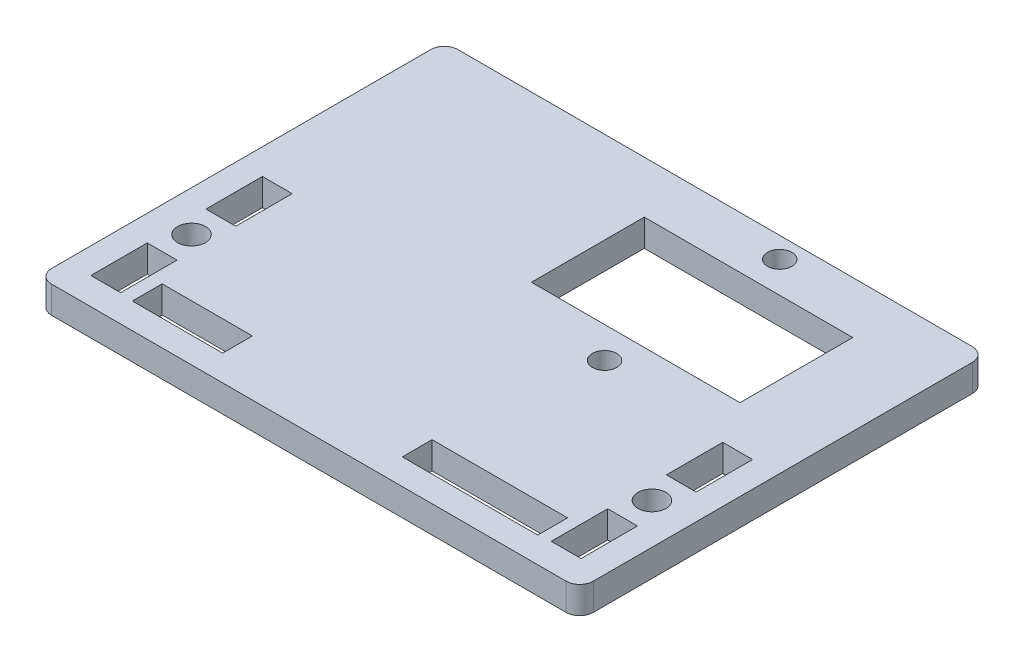
SolidWorks part; units mm, degrees
ref_plane "Front Plane" through (0, 0, 0) normal (0, 0, 1) x (1, 0, 0)
ref_plane "Top Plane" through (0, 0, 0) normal (0, 1, 0) x (1, 0, 0)
ref_plane "Right Plane" through (0, 0, 0) normal (1, 0, 0) x (0, 0, -1)
sketch "Sketch1" plane through (0, 0, 0) normal (0, 1, 0) x (1, 0, 0)
  line L1 (1.5, 0) -> (58.5, 0)
  line L2 (0, 1.5) -> (0, 43.5)
  line L3 (1.5, 45) -> (58.5, 45)
  line L4 (60, 1.5) -> (60, 43.5)
  arc A0 (1.5, 0) -> (0, 1.5) centre (1.5, 1.5) cw
  arc A1 (58.5, 0) -> (60, 1.5) centre (58.5, 1.5) ccw
  arc A2 (58.5, 45) -> (60, 43.5) centre (58.5, 43.5) cw
  arc A3 (0, 43.5) -> (1.5, 45) centre (1.5, 43.5) cw
  point P7 (0, 0)
  point P12 (60, 45)
  point P15 (0, 45)
  dimension "D3" = 1.5
  dimension "D1" = 45
  dimension "D2" = 60
extrude "Boss-Extrude1" add sketch "Sketch1" along normal blind 3
sketch "Sketch2" plane through (0, 3, 0) normal (0, 1, 0) x (1, 0, 0)
  line L0 (60, 1.5) -> (60, 43.5) construction
  line L1 (27.9, 39.25) -> (51, 39.25)
  line L2 (27.9, 39.25) -> (27.9, 26.75)
  line L3 (27.9, 26.75) -> (51, 26.75)
  line L4 (51, 39.25) -> (51, 26.75)
  line L5 (37.5, 6) -> (52.5, 6)
  line L6 (37.5, 6) -> (37.5, 3)
  line L7 (37.5, 3) -> (52.5, 3)
  line L8 (52.5, 6) -> (52.5, 3)
  line L9 (7.6, 6) -> (17.6, 6)
  line L10 (7.6, 6) -> (7.6, 3)
  line L11 (7.6, 3) -> (17.6, 3)
  line L12 (17.6, 6) -> (17.6, 3)
  line L13 (3, 22) -> (6, 22)
  line L14 (3, 22) -> (3, 15.75)
  line L15 (3, 15.75) -> (6, 15.75)
  line L16 (6, 22) -> (6, 15.75)
  line L17 (3, 9.25) -> (6, 9.25)
  line L18 (3, 9.25) -> (3, 3)
  line L19 (3, 3) -> (6, 3)
  line L20 (6, 9.25) -> (6, 3)
  line L21 (57, 22) -> (54, 22)
  line L22 (57, 22) -> (57, 15.75)
  line L23 (57, 15.75) -> (54, 15.75)
  line L24 (54, 22) -> (54, 15.75)
  line L25 (57, 9.25) -> (54, 9.25)
  line L26 (57, 9.25) -> (57, 3)
  line L27 (57, 3) -> (54, 3)
  line L28 (54, 9.25) -> (54, 3)
  line L29 (58.5, 45) -> (1.5, 45) construction
  line L30 (39.45, 42.7) -> (39.45, 39.25) construction
  line L32 (0, 43.5) -> (0, 1.5) construction
  line L33 (1.5, 0) -> (58.5, 0) construction
  line L34 (55.5, 15.75) -> (55.5, 9.25) construction
  line L35 (4.5, 15.75) -> (4.5, 9.25) construction
  circle A0 centre (39.45, 23.3) radius 1.35
  circle A1 centre (39.45, 42.7) radius 1.35
  circle A2 centre (4.5, 12.5) radius 1.55
  circle A3 centre (55.5, 12.5) radius 1.55
  point P47 (4.5, 12.5)
  point P48 (4.5, 9.25)
  dimension "D5" = 2.7
  dimension "D6" = 3.45
  dimension "D8" = 3.1
  dimension "D1" = 23.1
  dimension "D2" = 9
  dimension "D3" = 12.5
  dimension "D4" = 5.75
  dimension "D7" = 3.45
  dimension "D9" = 6.25
  dimension "D10" = 3
  dimension "D11" = 3
  dimension "D12" = 3
  dimension "D13" = 23
  dimension "D14" = 3
  dimension "D15" = 3
  dimension "D16" = 3
  dimension "D17" = 3
  dimension "D18" = 1.6
  dimension "D19" = 10
  dimension "D20" = 3
  dimension "D21" = 15
  dimension "D22" = 1.5
extrude "Main Hole Extrude" cut sketch "Sketch2" against normal through all
sketch "Sketch3" plane through (0, 3, 0) normal (0, 1, 0) x (1, 0, 0)
  line L0 (52.5, 3) -> (52.5, 6) construction
  line L1 (7.6, 6) -> (17.6, 6)
  line L2 (7.6, 6) -> (7.6, 6.15)
  line L3 (7.6, 6.15) -> (17.6, 6.15)
  line L4 (17.6, 6) -> (17.6, 6.15)
  line L5 (7.6, 3) -> (17.6, 3)
  line L6 (7.6, 3) -> (7.6, 2.85)
  line L7 (7.6, 2.85) -> (17.6, 2.85)
  line L8 (17.6, 3) -> (17.6, 2.85)
  line L9 (37.5, 6) -> (52.5, 6)
  line L10 (37.5, 6) -> (37.5, 6.15)
  line L11 (37.5, 6.15) -> (52.5, 6.15)
  line L12 (52.5, 6) -> (52.5, 6.15)
  line L13 (37.5, 3) -> (52.5, 3)
  line L14 (37.5, 3) -> (37.5, 2.85)
  line L15 (37.5, 2.85) -> (52.5, 2.85)
  line L16 (52.5, 3) -> (52.5, 2.85)
  line L17 (17.6, 3) -> (17.6, 6) construction
  line L18 (6, 9.25) -> (3, 9.25) construction
  line L19 (6, 22) -> (6.15, 22)
  line L20 (6, 22) -> (6, 15.75)
  line L21 (6, 15.75) -> (6.15, 15.75)
  line L22 (6.15, 22) -> (6.15, 15.75)
  line L23 (3, 22) -> (2.85, 22)
  line L24 (3, 22) -> (3, 15.75)
  line L25 (3, 15.75) -> (2.85, 15.75)
  line L26 (2.85, 22) -> (2.85, 15.75)
  line L27 (6, 9.25) -> (6.15, 9.25)
  line L28 (6, 9.25) -> (6, 3)
  line L29 (6, 3) -> (6.15, 3)
  line L30 (6.15, 9.25) -> (6.15, 3)
  line L31 (3, 9.25) -> (2.85, 9.25)
  line L32 (3, 9.25) -> (3, 3)
  line L33 (3, 3) -> (2.85, 3)
  line L34 (2.85, 9.25) -> (2.85, 3)
  line L35 (3, 3) -> (6, 3) construction
  line L36 (3, 15.75) -> (6, 15.75) construction
  line L38 (54, 3) -> (57, 3) construction
  line L39 (54, 22) -> (53.85, 22)
  line L40 (54, 22) -> (54, 15.75)
  line L41 (54, 15.75) -> (53.85, 15.75)
  line L42 (53.85, 22) -> (53.85, 15.75)
  line L43 (57, 22) -> (57.15, 22)
  line L44 (57, 22) -> (57, 15.75)
  line L45 (57, 15.75) -> (57.15, 15.75)
  line L46 (57.15, 22) -> (57.15, 15.75)
  line L47 (57, 9.25) -> (57.15, 9.25)
  line L48 (57, 9.25) -> (57, 3)
  line L49 (57, 3) -> (57.15, 3)
  line L50 (57.15, 9.25) -> (57.15, 3)
  line L51 (54, 9.25) -> (53.85, 9.25)
  line L52 (54, 9.25) -> (54, 3)
  line L53 (54, 3) -> (53.85, 3)
  line L54 (53.85, 9.25) -> (53.85, 3)
  line L55 (54, 15.75) -> (57, 15.75) construction
  dimension "D1" = 0.15
  dimension "D2" = 0.15
  dimension "D3" = 0.15
extrude "Clearance Extrude" cut sketch "Sketch3" against normal through all
